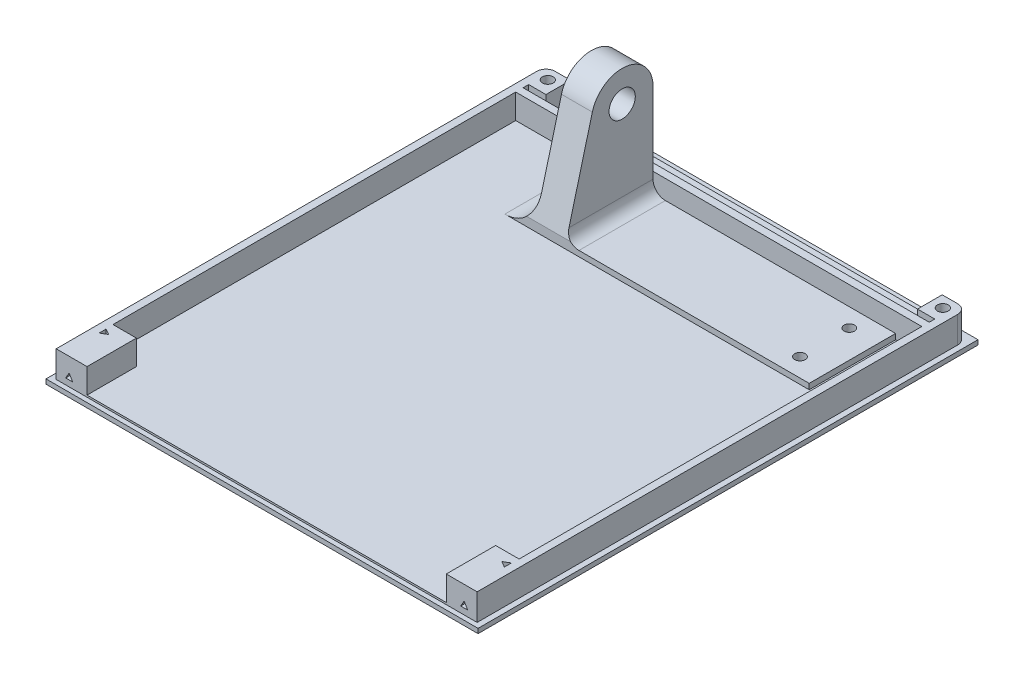
SolidWorks part; units mm, degrees
material "ABS"
ref_plane "Front" through (0, 0, 0) normal (0, 0, 1) x (1, 0, 0)
ref_plane "Top" through (0, 0, 0) normal (0, 1, 0) x (1, 0, 0)
ref_plane "Right" through (0, 0, 0) normal (1, 0, 0) x (0, 0, -1)
sketch "Croquis1" plane through (0, 0, 0) normal (0, 0, 1) x (1, 0, 0)
  line L0 (63.3, 3.9) -> (-15.3, 3.9)
  line L1 (-15.3, 3.9) -> (-15.3, 44)
  line L2 (-15.3, 44) -> (-25.3, 44)
  line L3 (-25.3, 44) -> (-25.3, 0)
  line L4 (-25.3, 0) -> (63.3, 0)
  line L6 (63.3, 3.9) -> (63.3, 0)
  dimension "D1" = 15.3
  dimension "D2" = 3.9
  dimension "D3" = 10
  dimension "D4" = 44
  dimension "D5" = 78.6
extrude "Saliente-Extruir1" add sketch "Croquis1" along normal blind 28
sketch "Croquis2" plane through (-25.3, 0, 0) normal (-1, 0, 0) x (0, 0, 1)
  line L0 (28, 5) -> (19.6686, 36.5529)
  line L1 (0, 44) -> (0, 0) construction
  line L2 (28, 44) -> (0, 44) construction
  line L3 (0, 34) -> (0, 33)
  line L4 (0, 33) -> (-1, 33)
  line L5 (-1, 33) -> (-1, 45)
  line L6 (-1, 45) -> (29, 45)
  line L7 (28, 5) -> (29, 5)
  line L8 (29, 5) -> (29, 45)
  line L9 (28, 44) -> (28, 0) construction
  line L10 (28, 0) -> (0, 0) construction
  arc A0 (19.6686, 36.5529) -> (0, 34) centre (10, 34) ccw
  circle A1 centre (10, 34) radius 4.25
  dimension "D4" = 8.5
  dimension "D5" = 10
  dimension "D1" = 1
  dimension "D2" = 1
  dimension "D3" = 1
  dimension "D6" = 5
extrude "Cortar-Extruir1" cut sketch "Croquis2" against normal through all
sketch "Croquis5" plane through (0, 0, 0) normal (0, 1, 0) x (1, 0, 0)
  line L1 (76, -148) -> (-64, -148)
  line L2 (76, -148) -> (76, 14)
  line L3 (76, 14) -> (-64, 14)
  line L4 (-64, -148) -> (-64, 14)
  line L5 (76, -148) -> (-64, 14) construction
  line L6 (76, 14) -> (-64, -148) construction
  line L7 (63.3, 0) -> (-15.3, 0) construction
  point P0 (63.3, 0)
  dimension "D1" = 140
  dimension "D2" = 162
  dimension "D4" = 14
extrude "PLACA-BASE" add sketch "Croquis5" along normal blind 2.1
fillet "Redondeo4" radius 10 1 edges at (-25.3, 2.1, 14)
fillet "Redondeo5" radius 4 1 edges at (-15.3, 3.9, 14)
sketch "Croquis6" plane through (0, 2.1, 0) normal (0, 1, 0) x (1, 0, 0)
  line L0 (-64, 14) -> (-64, -148) construction
  line L1 (74.2, -146.5) -> (-62.2, -146.5)
  line L2 (74.2, -146.5) -> (74.2, 12.2)
  line L3 (74.2, 12.2) -> (-62.2, 12.2)
  line L4 (-62.2, -146.5) -> (-62.2, 12.2)
  line L5 (74.2, -146.5) -> (-62.2, 12.2) construction
  line L6 (74.2, 12.2) -> (-62.2, -146.5) construction
  line L7 (76, 14) -> (-64, 14) construction
  line L8 (76, -148) -> (76, 14) construction
  line L9 (-64, -148) -> (76, -148) construction
  point P0 (6, -67.15)
  dimension "D1" = 1.8
  dimension "D2" = 1.8
  dimension "D3" = 1.8
  dimension "D4" = 1.5
extrude "Cortar-Extruir3" cut sketch "Croquis6" against normal blind 0.6 flip side to cut
ref_plane "Plano1" through (6, 0, 0) normal (-1, 0, 0) x (0, 0, 1)
sketch "Croquis8" plane through (0, 2.1, 0) normal (0, 1, 0) x (1, 0, 0)
  line L0 (76, -67.15) -> (45.9927, -67.15) construction
  line L1 (76, -148) -> (76, 14) construction
  line L2 (66.2, 12.2) -> (74.2, 12.2)
  line L3 (74.2, 12.2) -> (74.2, -146.5)
  line L4 (66.2, 12.2) -> (66.2, 4.2)
  line L5 (66.2, 4.2) -> (71.8, 4.2)
  line L6 (71.8, 4.2) -> (71.8, 2.4)
  line L7 (74.2, -146.5) -> (74.2, 12.2) construction
  line L8 (-62.2, -146.5) -> (74.2, -146.5) construction
  line L9 (64.2, -130.5) -> (71.8, -130.5)
  line L10 (64.2, -146.5) -> (64.2, -130.5)
  line L11 (64.2, -146.5) -> (74.2, -146.5)
  line L12 (6, 0.825) -> (6, -0.825) construction
  line L13 (74.2, 12.2) -> (-62.2, 12.2) construction
  line L14 (71.8, 0) -> (6, 0)
  line L16 (71.8, 2.4) -> (6, 2.4)
  line L17 (6, 0) -> (6, 2.4)
  line L18 (71.8, 0) -> (71.8, -130.5)
  line L19 (63.3, 0) -> (-35.3, 0) construction
  point P19 (74.2, -67.15)
  dimension "D6" = 16
  dimension "D7" = 10
  dimension "D1" = 2.4
  dimension "D2" = 8
  dimension "D3" = 8
  dimension "D4" = 2.4
extrude "Saliente-Extruir2" add sketch "Croquis8" along normal blind 8
ref_plane "Plano2" through (0, 0, 67.15) normal (0, 0, 1) x (1, 0, 0)
sketch "Croquis9" plane through (0, 0, 146.5) normal (0, 0, 1) x (1, 0, 0)
  line L8 (-64, 0) -> (76, 0) construction
  line L9 (70, 5.4) -> (68.8742, 3.45)
  line L10 (68.8742, 3.45) -> (71.1258, 3.45)
  line L11 (71.1258, 3.45) -> (70, 5.4)
  line L12 (76, 1.5) -> (76, 0) construction
  circle A0 centre (70, 4.1) radius 1.3 construction
  dimension "D1" = 2.6
  dimension "D2" = 4.1
  dimension "D3" = 6
extrude "TORNILLOS-BAE" cut sketch "Croquis9" against normal offset from surface (14 mm away) 2 up to face at (68, 6.1, 130.5)
sketch "Croquis10" plane through (0, 10.1, 0) normal (0, 1, 0) x (1, 0, 0)
  line L0 (76, -148) -> (76, 14) construction
  line L1 (76, 14) -> (-64, 14) construction
  circle A0 centre (70, 8.6) radius 1.75
  dimension "D1" = 3.5
  dimension "D2" = 6
  dimension "D3" = 5.4
extrude "Cortar-Extruir6" cut sketch "Croquis10" against normal up to next (10.1 mm away)
sketch "Croquis3" plane through (0, 0, 0) normal (0, -1, 0) x (1, 0, 0)
  line L0 (63.3, 28) -> (63.3, 0) construction
  line L1 (72.3, 6) -> (54.3, 6) construction
  line L2 (72.3, 6) -> (72.3, 22) construction
  line L3 (72.3, 22) -> (54.3, 22) construction
  line L4 (54.3, 6) -> (54.3, 22) construction
  line L5 (72.3, 6) -> (54.3, 22) construction
  line L6 (72.3, 22) -> (54.3, 6) construction
  circle A0 centre (54.3, 22) radius 1.7
  circle A1 centre (54.3, 6) radius 1.7
  point P0 (63.3, 14)
  dimension "D1" = 3.4
  dimension "D2" = 16
  dimension "D3" = 18
extrude "MOT-SOP-NEMA" cut sketch "Croquis3" against normal up to next
sketch "Croquis11" plane through (0, 10.1, 0) normal (0, 1, 0) x (1, 0, 0)
  line L0 (76, -148) -> (76, 14) construction
  line L1 (69.7, -134) -> (71.65, -135.1258)
  line L2 (71.65, -135.1258) -> (71.65, -132.8742)
  line L3 (71.65, -132.8742) -> (69.7, -134)
  line L4 (-64, -148) -> (76, -148) construction
  circle A0 centre (71, -134) radius 1.3 construction
  dimension "D1" = 2.6
  dimension "D2" = 5
  dimension "D3" = 14
extrude "Cortar-Extruir7" cut sketch "Croquis11" against normal up to next
mirror "Simetría3" about plane through (6, 0, 0) normal (-1, 0, 0) of "Cortar-Extruir7", "Saliente-Extruir2", "TORNILLOS-BAE", "Cortar-Extruir6"
fillet "Redondeo3" radius 3 2 edges at (74.2, 5.8, -12.2) (-62.2, 5.8, -12.2)
